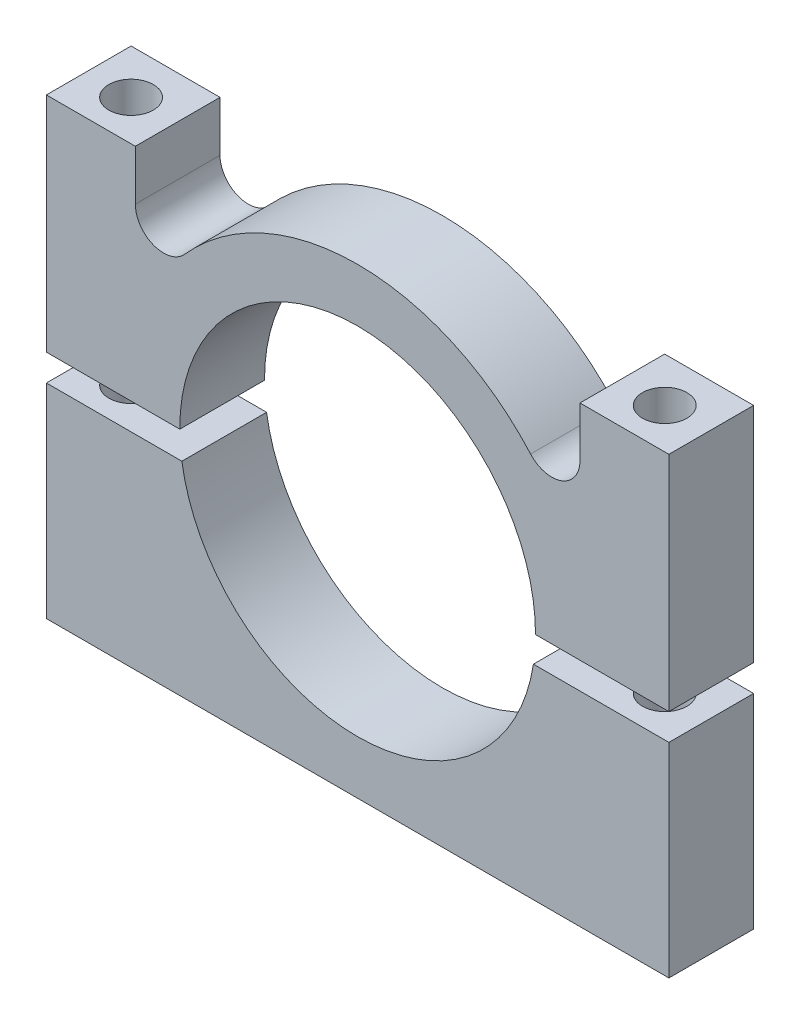
SolidWorks part; units mm, degrees
ref_plane "Front Plane" through (0, 0, 0) normal (0, 0, 1) x (1, 0, 0)
ref_plane "Top Plane" through (0, 0, 0) normal (0, 1, 0) x (1, 0, 0)
ref_plane "Right Plane" through (0, 0, 0) normal (1, 0, 0) x (0, 0, -1)
sketch "Sketch1" plane through (0, 0, 0) normal (0, 0, 1) x (1, 0, 0)
  line L0 (-17.5, 12.5) -> (-12.5, 12.5)
  line L1 (17.5, 12.5) -> (17.5, -0.0265)
  line L2 (17.5, -13) -> (-17.5, -13)
  line L3 (-17.5, -13) -> (-17.5, -1.5265)
  line L4 (-12.5, 12.5) -> (-12.5, -13) construction
  line L5 (12.5, 12.5) -> (12.5, -13) construction
  line L6 (12.5, 12.5) -> (17.5, 12.5)
  line L7 (-17.5, -0.0265) -> (17.5, -0.0265) construction
  line L8 (-17.5, -1.5265) -> (17.5, -1.5265) construction
  line L9 (-12.5, 12.5) -> (-12.5, 9.6805)
  line L10 (12.5, 12.5) -> (12.5, 9.6805)
  line L11 (-17.5, -0.0265) -> (-17.5, 12.5)
  line L12 (17.5, -1.5265) -> (17.5, -13)
  line L13 (-17.5, -0.0265) -> (-10, -0.0265)
  line L14 (10, -0.0265) -> (17.5, -0.0265)
  line L15 (17.5, -1.5265) -> (9.8828, -1.5265)
  line L16 (-9.8828, -1.5265) -> (-17.5, -1.5265)
  arc A0 (-9.8828, -1.5265) -> (9.8828, -1.5265) centre (0, 0) ccw
  arc A1 (10, -0.0265) -> (-10, -0.0265) centre (0, 0) ccw
  arc A2 (9.7249, 8.627) -> (-9.7249, 8.627) centre (0, 0) ccw
  arc A3 (12.5, 9.6805) -> (9.7249, 8.627) centre (10.9125, 9.6805) cw
  arc A4 (-9.7249, 8.627) -> (-12.5, 9.6805) centre (-10.9125, 9.6805) cw
  point P5 (-10, 0)
  point P8 (10, 0)
  point P9 (0, -10)
  point P10 (0, 10)
  point P11 (-12.5, 12.5)
  point P12 (12.5, 12.5)
  point P13 (12.5, -13)
  point P14 (-12.5, -13)
  point P25 (-17.5, -0.7765)
  point P29 (0, 13)
  point P32 (12.5, 3.5707)
  point P35 (-12.5, 3.5707)
  dimension "D1" = 7.5
  dimension "D9" = 3
  dimension "D10" = 1.5875
  dimension "D2" = 7.5
  dimension "D3" = 3
  dimension "D4" = 2.5
  dimension "D5" = 5
  dimension "D6" = 5
  dimension "D7" = 0.75
  dimension "D8" = 0.75
extrude "Boss-Extrude1" add sketch "Sketch1" along normal blind 4.763
hole_wizard "Tap Drill for M3x0.5 Tap2" positions "Sketch5" profile "Sketch4" hole size "M3x0.5" standard "ANSI Metric" end condition through all
sketch "Sketch5" plane through (0, 12.5, 0) normal (0, 1, 0) x (1, 0, 0)
  line L0 (-17.5, -4.763) -> (-17.5, 0) construction
  line L1 (-12.5, 0) -> (-17.5, 0) construction
  point P0 (-15.0028, -2.5)
  point P3 (-17.5, -2.3815)
  point P6 (-15, 0)
  dimension "D1" = 2.5
  dimension "D2" = 2.5
sketch "Sketch4" plane through (-15.0028, 12.5, 2.5) normal (1, 0, 0) x (0, 0, 1)
  line L0 (0, 0) -> (0, 25.5)
  line L1 (0, 25.5) -> (1.25, 25.5)
  line L2 (1.25, 25.5) -> (1.25, 0)
  line L5 (1.25, 0) -> (0, 0)
  line L11 (0, -6.35) -> (0, 107.95) construction
  dimension "Thru Hole Dia." = 2.5
  dimension "Thru Hole Depth" = 25.5
hole_wizard "Tap Drill for M3x0.5 Tap3" positions "Sketch7" profile "Sketch6" hole size "M3x0.5" standard "ANSI Metric" end condition through all
sketch "Sketch7" plane through (0, 12.5, 0) normal (0, 1, 0) x (1, 0, 0)
  line L0 (17.5, 0) -> (12.5, 0) construction
  line L1 (17.5, -4.763) -> (17.5, 0) construction
  point P0 (15.0028, -2.5)
  point P3 (15, 0)
  point P6 (17.5, -2.3815)
  dimension "D1" = 2.5
  dimension "D2" = 2.5
sketch "Sketch6" plane through (15.0028, 12.5, 2.5) normal (1, 0, 0) x (0, 0, 1)
  line L0 (0, 0) -> (0, 25.5)
  line L1 (0, 25.5) -> (1.25, 25.5)
  line L2 (1.25, 25.5) -> (1.25, 0)
  line L5 (1.25, 0) -> (0, 0)
  line L11 (0, -6.35) -> (0, 107.95) construction
  dimension "Thru Hole Dia." = 2.5
  dimension "Thru Hole Depth" = 25.5
